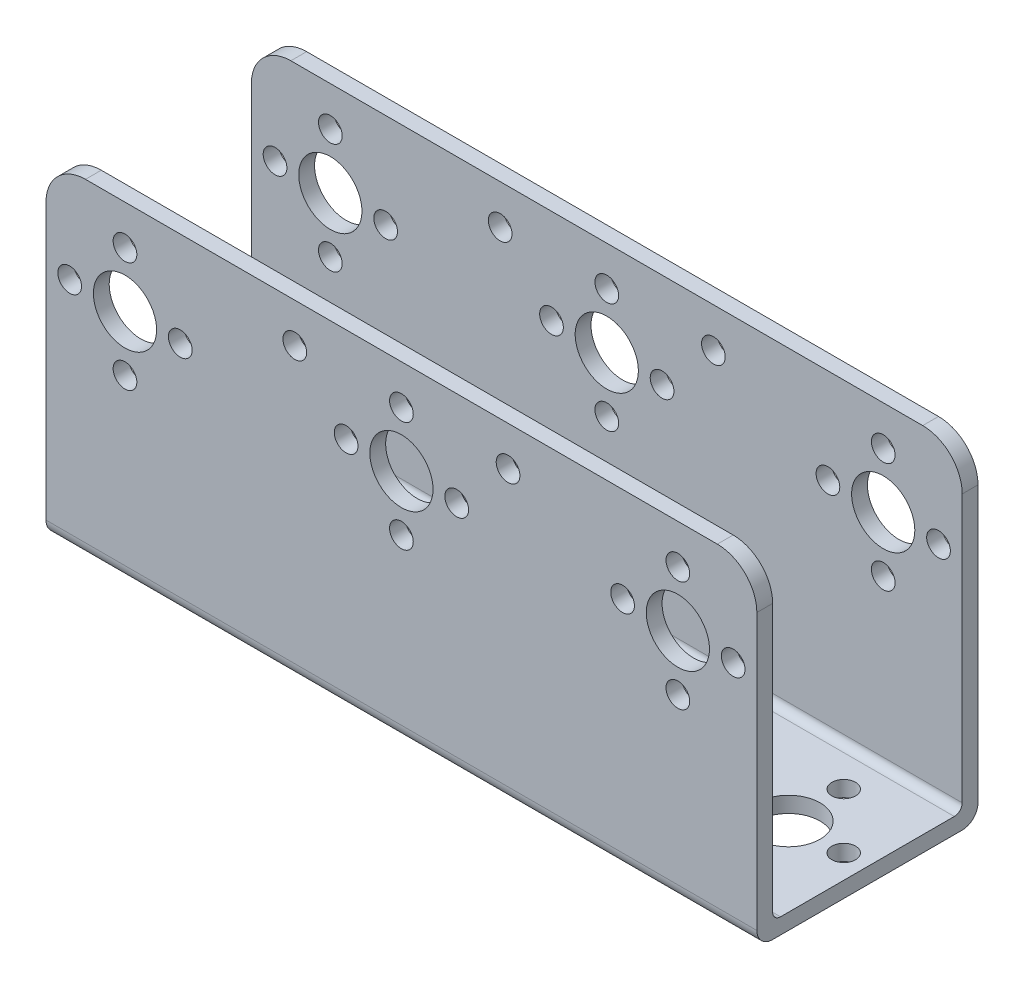
SolidWorks part; units mm, degrees
ref_plane "Piano frontale" through (0, 0, 0) normal (0, 0, 1) x (1, 0, 0)
ref_plane "Piano superiore" through (0, 0, 0) normal (0, 1, 0) x (1, 0, 0)
ref_plane "Piano destro" through (0, 0, 0) normal (1, 0, 0) x (0, 0, -1)
sketch "Schizzo1" plane through (0, 0, 0) normal (0, 0, 1) x (1, 0, 0)
  line L1 (0, 0) -> (90, 0)
  line L2 (0, 0) -> (0, 36.8605)
  line L3 (5, 41.8605) -> (85, 41.8605)
  line L4 (90, 0) -> (90, 36.8605)
  arc A0 (85, 41.8605) -> (90, 36.8605) centre (85, 36.8605) cw
  arc A1 (0, 36.8605) -> (5, 41.8605) centre (5, 36.8605) cw
  point P7 (90, 41.8605)
  point P10 (0, 41.8605)
  dimension "D3" = 5
  dimension "D1" = 90
  dimension "D2" = 41.8605
extrude "Estrusione-Estrusione1" add sketch "Schizzo1" against normal blind 2
sketch "Schizzo2" plane through (0, 0, 0) normal (0, 1, 0) x (1, 0, 0)
  line L1 (0, 0) -> (90, 0)
  line L2 (0, 0) -> (0, 28)
  line L3 (0, 28) -> (90, 28)
  line L4 (90, 0) -> (90, 28)
  dimension "D1" = 90
  dimension "D2" = 28
extrude "Estrusione-Estrusione2" add sketch "Schizzo2" along normal blind 2
ref_plane "Piano1" through (0, 0, -28) normal (0, 0, 1) x (1, 0, 0)
sketch "Schizzo4" plane through (0, 0, -28) normal (0, 0, 1) x (1, 0, 0)
  line L4 (90, 0) -> (90, 36.8605)
  line L5 (85, 41.8605) -> (5, 41.8605)
  line L6 (0, 36.8605) -> (0, 0)
  line L7 (0, 0) -> (90, 0)
  line L8 (90, 0) -> (90, 36.8605)
  line L9 (85, 41.8605) -> (5, 41.8605)
  line L10 (0, 36.8605) -> (0, 0)
  line L11 (0, 0) -> (90, 0)
  arc A2 (90, 36.8605) -> (85, 41.8605) centre (85, 36.8605) ccw
  arc A3 (5, 41.8605) -> (0, 36.8605) centre (5, 36.8605) ccw
  arc A4 (90, 36.8605) -> (85, 41.8605) centre (85, 36.8605) ccw
  arc A5 (5, 41.8605) -> (0, 36.8605) centre (5, 36.8605) ccw
  dimension "D1" = 0
extrude "Estrusione-Estrusione3" add sketch "Schizzo4" along normal blind 2
sketch "Schizzo5" plane through (0, 0, 0) normal (0, 0, 1) x (1, 0, 0)
  line L0 (10, 22.8605) -> (45, 22.8605) construction
  line L1 (85, 41.8605) -> (5, 41.8605) construction
  line L2 (0, 36.8605) -> (0, 0) construction
  line L3 (10, 29.8605) -> (45, 29.8605) construction
  line L4 (90, 0) -> (90, 36.8605) construction
  line L5 (45, 29.8605) -> (80, 29.8605) construction
  line L6 (45, 22.8605) -> (80, 22.8605) construction
  line L7 (10, 36.8605) -> (45, 36.8605) construction
  line L8 (45, 36.8605) -> (80, 36.8605) construction
  circle A0 centre (10, 29.8605) radius 4
  circle A1 centre (45, 29.8605) radius 4
  circle A2 centre (80, 29.8605) radius 4
  circle A3 centre (10, 36.8605) radius 1.5
  circle A4 centre (3, 29.8605) radius 1.5
  circle A5 centre (10, 22.8605) radius 1.5
  circle A6 centre (17, 29.8605) radius 1.5
  circle A7 centre (38, 29.8605) radius 1.5
  circle A8 centre (45, 36.8605) radius 1.5
  circle A9 centre (80, 36.8605) radius 1.5
  circle A10 centre (73, 29.8605) radius 1.5
  circle A11 centre (45, 22.8605) radius 1.5
  circle A12 centre (80, 22.8605) radius 1.5
  circle A13 centre (87, 29.8605) radius 1.5
  circle A16 centre (52, 29.8605) radius 1.5
  dimension "D1" = 8
  dimension "D2" = 7
  dimension "D3" = 7
  dimension "D4" = 7
  dimension "D5" = 3
  dimension "D6" = 7
  dimension "D7" = 7
  dimension "D8" = 7
  dimension "D9" = 7
  dimension "D10" = 7
  dimension "D11" = 7
  dimension "D12" = 7
  dimension "D13" = 7
  dimension "D14" = 7
  dimension "D15" = 12
  dimension "D16" = 10
  dimension "D17" = 10
  dimension "D18" = 3
  dimension "D19" = 3
extrude "Taglio-Estrusione1" cut sketch "Schizzo5" against normal through all
fillet "Raccordo1" radius 2 1 edges at (45, 0, -28)
fillet "Raccordo2" radius 2 1 edges at (45, 0, 0)
fillet "Raccordo3" radius 1 1 edges at (45, 2, -2)
fillet "Raccordo4" radius 1 1 edges at (45, 2, -26)
sketch "Schizzo6" plane through (0, 0, 0) normal (0, 1, 0) x (1, 0, 0)
  line L0 (0, 14) -> (90, 14) construction
  line L1 (0, 25) -> (0, 3) construction
  line L2 (90, 3) -> (90, 25) construction
  line L3 (10, 3) -> (10, 14) construction
  line L4 (0, 3) -> (90, 3) construction
  line L5 (10, 14) -> (10, 25) construction
  line L6 (90, 25) -> (0, 25) construction
  line L7 (45, 3) -> (45, 14) construction
  line L8 (45, 14) -> (45, 25) construction
  line L9 (80, 3) -> (80, 14) construction
  line L10 (80, 14) -> (80, 25) construction
  circle A0 centre (45, 14) radius 4
  circle A1 centre (10, 14) radius 4
  circle A2 centre (80, 14) radius 4
  circle A3 centre (10, 21) radius 1.5
  circle A4 centre (3, 14) radius 1.5
  circle A5 centre (10, 7) radius 1.5
  circle A6 centre (17, 14) radius 1.5
  circle A7 centre (38, 14) radius 1.5
  circle A8 centre (45, 21) radius 1.5
  circle A9 centre (80, 21) radius 1.5
  circle A10 centre (80, 7) radius 1.5
  circle A11 centre (45, 7) radius 1.5
  circle A12 centre (52, 14) radius 1.5
  circle A13 centre (87, 14) radius 1.5
  circle A14 centre (73, 14) radius 1.5
  dimension "D1" = 8
  dimension "D4" = 3
  dimension "D2" = 10
  dimension "D3" = 10
  dimension "D5" = 7
  dimension "D6" = 7
  dimension "D7" = 7
  dimension "D8" = 7
  dimension "D9" = 7
  dimension "D10" = 7
  dimension "D11" = 7
  dimension "D12" = 7
  dimension "D13" = 7
  dimension "D14" = 7
  dimension "D15" = 7
  dimension "D16" = 7
extrude "Taglio-Estrusione2" cut sketch "Schizzo6" along normal through all
sketch "Sketch1" plane through (0, 0, 0) normal (0, 0, 1) x (1, 0, 0)
  line L0 (85, 41.8605) -> (5, 41.8605) construction
  line L1 (45, 36.8605) -> (45, 41.8605) construction
  line L2 (45, 36.8605) -> (45, 22.8605) construction
  circle A0 centre (31.5, 36.8605) radius 1.5
  circle A1 centre (58.5, 36.8605) radius 1.5
  dimension "D1" = 3
  dimension "D2" = 3
  dimension "D3" = 5
  dimension "D4" = 5
  dimension "D5" = 13.5
  dimension "D6" = 13.5
extrude "Cut-Extrude1" cut sketch "Sketch1" against normal through all both and the other way through all
